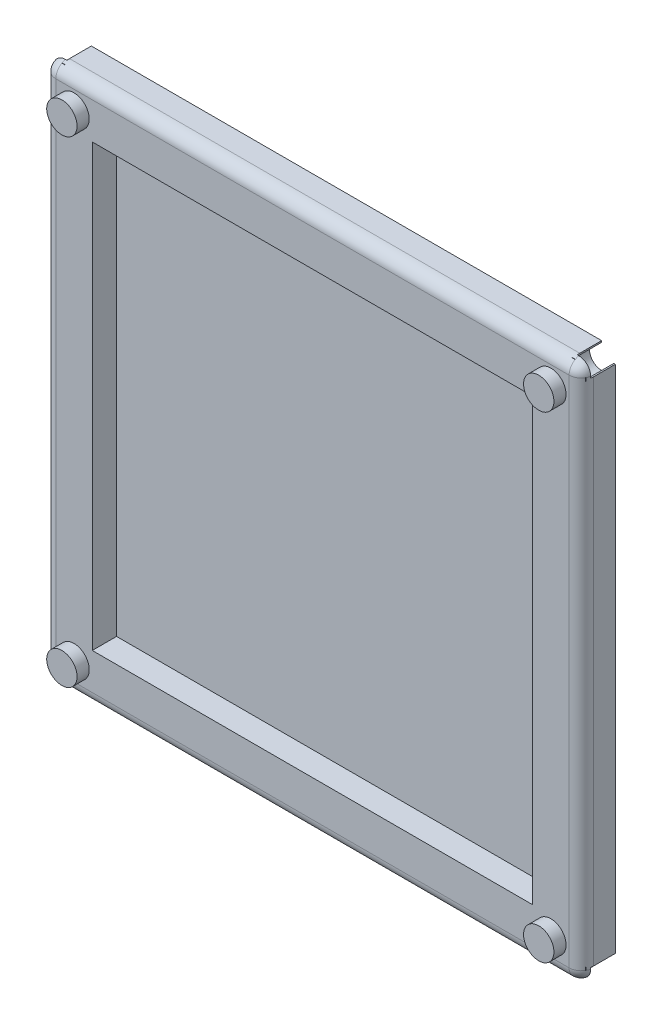
SolidWorks part; units mm, degrees
ref_plane "Front Plane" through (0, 0, 0) normal (0, 0, 1) x (1, 0, 0)
ref_plane "Top Plane" through (0, 0, 0) normal (0, 1, 0) x (1, 0, 0)
ref_plane "Right Plane" through (0, 0, 0) normal (1, 0, 0) x (0, 0, -1)
sketch "Sketch1" plane through (0, 0, 0) normal (0, 0, 1) x (1, 0, 0)
  line L1 (0, 0) -> (-88.5, 0)
  line L2 (0, 0) -> (0, -88.5)
  line L3 (0, -88.5) -> (-88.5, -88.5)
  line L4 (-88.5, 0) -> (-88.5, -88.5)
  line L5 (0, 0) -> (-88.5, -88.5) construction
  line L6 (0, -88.5) -> (-88.5, 0) construction
  line L10 (0, -88.5) -> (-88.5, -88.5)
  line L11 (-88.5, 0) -> (-88.5, -88.5)
  line L12 (0, 0) -> (-88.5, 0)
  line L13 (0, 0) -> (0, -88.5)
  circle A4 centre (-86.25, -86.25) radius 2
  circle A5 centre (-2.25, -86.25) radius 2
  circle A6 centre (-2.25, -2.25) radius 2
  circle A7 centre (-86.25, -2.25) radius 2
  point P4 (-44.25, -44.25)
  point P14 (0, 0)
  point P16 (-86.29, -2.2649)
  dimension "D3" = 4
  dimension "D4" = 4
  dimension "D5" = 4
  dimension "D6" = 4
  dimension "D1" = 88.5
  dimension "D2" = 88.5
  dimension "D7" = 2.25
  dimension "D8" = 2.25
  dimension "D9" = 2.25
  dimension "D10" = 2.25
  dimension "D11" = 2.25
  dimension "D12" = 2.25
  dimension "D13" = 2.25
  dimension "D14" = 2.25
  dimension "D15" = 88.5
extrude "Boss-Extrude1" add sketch "Sketch1" along normal blind 4.6
sketch "Sketch2" plane through (0, 0, 4.6) normal (0, 0, 1) x (1, 0, 0)
  line L0 (0, -88.5) -> (-88.5, -88.5) construction
  line L1 (0, 0) -> (0, -88.5) construction
  line L2 (-88.5, 0) -> (-88.5, -88.5) construction
  line L3 (0, 0) -> (0, -88.5) construction
  line L4 (0, 0) -> (-88.5, 0) construction
  line L5 (-88.5, 0) -> (-88.5, -88.5) construction
  circle A0 centre (-5, -83.5) radius 2.5
  circle A1 centre (-83.5, -83.5) radius 2.5
  circle A2 centre (-5, -5) radius 2.5
  circle A3 centre (-83.5, -5) radius 2.5
  dimension "D1" = 5
  dimension "D2" = 5
  dimension "D3" = 5
  dimension "D4" = 5
  dimension "D5" = 5
  dimension "D6" = 5
  dimension "D7" = 5
  dimension "D8" = 5
  dimension "D9" = 5
  dimension "D10" = 5
  dimension "D11" = 5
  dimension "D12" = 5
extrude "Boss-Extrude2" add sketch "Sketch2" along normal blind 3
sketch "Sketch3" plane through (0, 0, 4.6) normal (0, 0, 1) x (1, 0, 0)
  line L1 (-88.5, 0) -> (0, 0)
  line L2 (-88.5, 0) -> (-88.5, -88.5)
  line L3 (-88.5, -88.5) -> (0, -88.5)
  line L4 (0, 0) -> (0, -88.5)
  line L5 (-88.5, 0) -> (0, -88.5) construction
  line L6 (-88.5, -88.5) -> (0, 0) construction
  point P4 (-44.25, -44.25)
extrude "Boss-Extrude3" add sketch "Sketch3" along normal blind 1
fillet "Fillet1" radius 2 8 edges at (-88.5, -44.25, 5.6) (-44.25, 0, 5.6) (0, -44.25, 5.6) (-44.25, -88.5, 5.6) (-88.5, -88.5, 2.8) (0, -88.5, 2.8) (-88.5, 0, 2.8) (0, 0, 2.8)
sketch "Sketch4" plane through (0, 0, 0) normal (0, 0, -1) x (-1, 0, 0)
  line L1 (86.25, -86.25) -> (88.5, -86.25)
  line L2 (86.25, -86.25) -> (86.25, -88.5)
  line L3 (86.25, -88.5) -> (88.5, -88.5)
  line L4 (88.5, -86.25) -> (88.5, -88.5)
  line L5 (86.25, -86.25) -> (88.5, -88.5) construction
  line L6 (86.25, -88.5) -> (88.5, -86.25) construction
  line L7 (2.25, -86.25) -> (0, -86.25)
  line L8 (2.25, -86.25) -> (2.25, -88.5)
  line L9 (2.25, -88.5) -> (0, -88.5)
  line L10 (0, -86.25) -> (0, -88.5)
  line L11 (2.25, -86.25) -> (0, -88.5) construction
  line L12 (2.25, -88.5) -> (0, -86.25) construction
  line L13 (86.25, -2.25) -> (88.5, -2.25)
  line L14 (86.25, -2.25) -> (86.25, 0)
  line L15 (86.25, 0) -> (88.5, 0)
  line L16 (88.5, -2.25) -> (88.5, 0)
  line L17 (86.25, -2.25) -> (88.5, 0) construction
  line L18 (86.25, 0) -> (88.5, -2.25) construction
  line L19 (2.25, -2.25) -> (0, -2.25)
  line L20 (2.25, -2.25) -> (2.25, 0)
  line L21 (2.25, 0) -> (0, 0)
  line L22 (0, -2.25) -> (0, 0)
  line L23 (2.25, -2.25) -> (0, 0) construction
  line L24 (2.25, 0) -> (0, -2.25) construction
  point P4 (87.375, -87.375)
  point P11 (1.125, -87.375)
  point P18 (87.375, -1.125)
  point P25 (1.125, -1.125)
extrude "Cut-Extrude1" cut sketch "Sketch4" against normal blind 4
sketch "Sketch5" plane through (0, 0, 5.6) normal (0, 0, 1) x (1, 0, 0)
  line L0 (0, -88.5) -> (-88.5, 0) construction
  line L1 (-80.5, -8) -> (-8, -8)
  line L2 (-80.5, -8) -> (-80.5, -80.5)
  line L3 (-80.5, -80.5) -> (-8, -80.5)
  line L4 (-8, -8) -> (-8, -80.5)
  line L5 (-80.5, -8) -> (-8, -80.5) construction
  line L6 (-80.5, -80.5) -> (-8, -8) construction
  line L7 (-2, -86.5) -> (-2, -2) construction
  point P0 (-44.25, -44.25)
  dimension "D1" = 6
extrude "Cut-Extrude2" cut sketch "Sketch5" against normal blind 4
